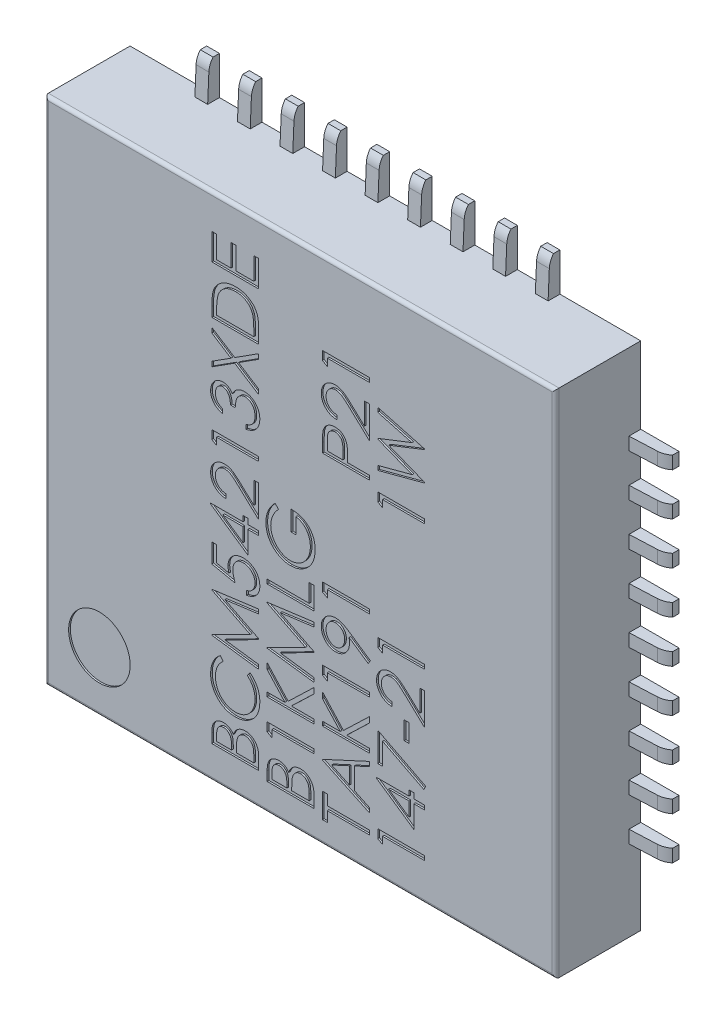
SolidWorks part; units mm, degrees
ref_plane "Płaszczyzna przednia" through (0, 0, 0) normal (0, 0, 1) x (1, 0, 0)
ref_plane "Płaszczyzna górna" through (0, 0, 0) normal (0, 1, 0) x (1, 0, 0)
ref_plane "Płaszczyzna prawa" through (0, 0, 0) normal (1, 0, 0) x (0, 0, -1)
sketch "Sketch1" plane through (0, 0, 0) normal (0, 0, 1) x (1, 0, 0)
  line L1 (3, -3) -> (-3, -3)
  line L2 (3, -3) -> (3, 3)
  line L3 (3, 3) -> (-3, 3)
  line L4 (-3, -3) -> (-3, 3)
  line L5 (3, -3) -> (-3, 3) construction
  line L6 (3, 3) -> (-3, -3) construction
  point P0 (0, 0)
extrude "Boss-Extrude1" add sketch "Sketch1" along normal blind 1
fillet "Fillet1" radius 0.04 4 edges at (0, 3, 1) (3, 0, 1) (0, -3, 1) (-3, 0, 1)
sketch "Sketch2" plane through (0, 0, 1) normal (0, 0, 1) x (1, 0, 0)
  line L0 (-0.4896, -2.96) -> (-0.4896, 2.8946) construction
  line L1 (-2.96, -2.96) -> (2.96, -2.96) construction
  line L2 (0.1604, -2.96) -> (0.1604, 2.8946) construction
  line L3 (0.8104, -2.96) -> (0.8104, 2.8946) construction
  line L4 (1.4604, -2.96) -> (1.4604, 2.8946) construction
  circle A0 centre (-2.3603, -2.3006) radius 0.3617
  text T0 "BCM54213XDE" font "Century Gothic" height 0.55
  text T1 " B1KMLG" font "Century Gothic" height 0.55
  text T2 " TAK191     P21" font "Century Gothic" height 0.55
  text T3 " 147-21     1W" font "Century Gothic" height 0.55
  dimension "D1" = 4
extrude "Cut-Extrude1" cut sketch "Sketch2" against normal blind 0.02
sketch "Sketch3" plane through (0, 0, 0) normal (0, 0, -1) x (-1, 0, 0)
  line L0 (2.05, -3) -> (2.05, -3.45)
  line L1 (-3, -3) -> (3, -3) construction
  line L2 (2.05, -3.45) -> (1.9, -3.45)
  line L3 (1.9, -3.45) -> (1.9, -3)
  line L4 (1.9, -3) -> (2.05, -3)
  line L5 (3, -3) -> (3, 3) construction
  dimension "D1" = 0.95
  dimension "D2" = 0.15
  dimension "D3" = 0.45
extrude "Boss-Extrude2" add sketch "Sketch3" against normal blind 0.15 separate body
sketch "Sketch4" plane through (-2.05, 0, 0) normal (-1, 0, 0) x (0, 0, 1)
  line L0 (0.1384, -3) -> (0.1243, -3.322)
  line L1 (0.96, -3) -> (0, -3) construction
  line L2 (0.15, -3.45) -> (0, -3.45) construction
  line L3 (0.1384, -3) -> (0.232, -3)
  line L4 (0.232, -3) -> (0.1922, -3.6098)
  line L5 (0.1922, -3.6098) -> (0.1134, -3.5357)
  line L6 (0.1134, -3.5357) -> (0.075, -3.45)
  arc A0 (0.1243, -3.322) -> (0.075, -3.45) centre (-0.0907, -3.3126) cw
extrude "Cut-Extrude2" cut sketch "Sketch4" against normal through all
pattern_linear "LPattern1" count 9 spacing 0.5 along (1, 0, 0) of bodies 104
sketch "Sketch5" plane through (0, 0, 0) normal (0, 0, -1) x (-1, 0, 0)
  circle A0 centre (0, 0) radius 2.5
  dimension "D1" = 5
extrude "Boss-Extrude3" add sketch "Sketch5" along normal blind 0.1 separate body
pattern_circular "CirPattern1" count 4 over 360 about axis through (0, 0, 0) along (0, 0, 1) of bodies 112 111 110 109 108 107 106 105 104
